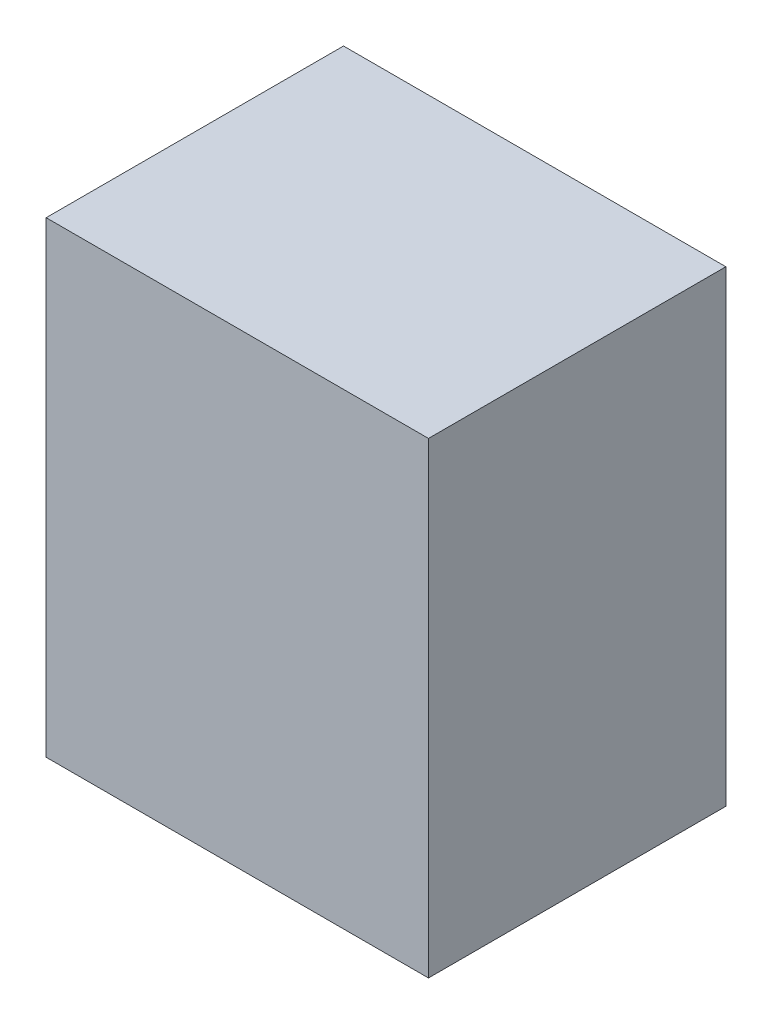
SolidWorks part; units mm, degrees
ref_plane "Plan de face" through (0, 0, 0) normal (0, 0, 1) x (1, 0, 0)
ref_plane "Plan de dessus" through (0, 0, 0) normal (0, 1, 0) x (1, 0, 0)
ref_plane "Plan de droite" through (0, 0, 0) normal (1, 0, 0) x (0, 0, -1)
sketch "Esquisse1" plane through (0, 0, 0) normal (0, 0, 1) x (1, 0, 0)
  line L1 (-38.0085, 31.9565) -> (51.9915, 31.9565)
  line L2 (-38.0085, 31.9565) -> (-38.0085, -78.0435)
  line L3 (-38.0085, -78.0435) -> (51.9915, -78.0435)
  line L4 (51.9915, 31.9565) -> (51.9915, -78.0435)
  dimension "D1" = 90
  dimension "D2" = 110
extrude "Boss.-Extru.1" add sketch "Esquisse1" along normal blind 70
